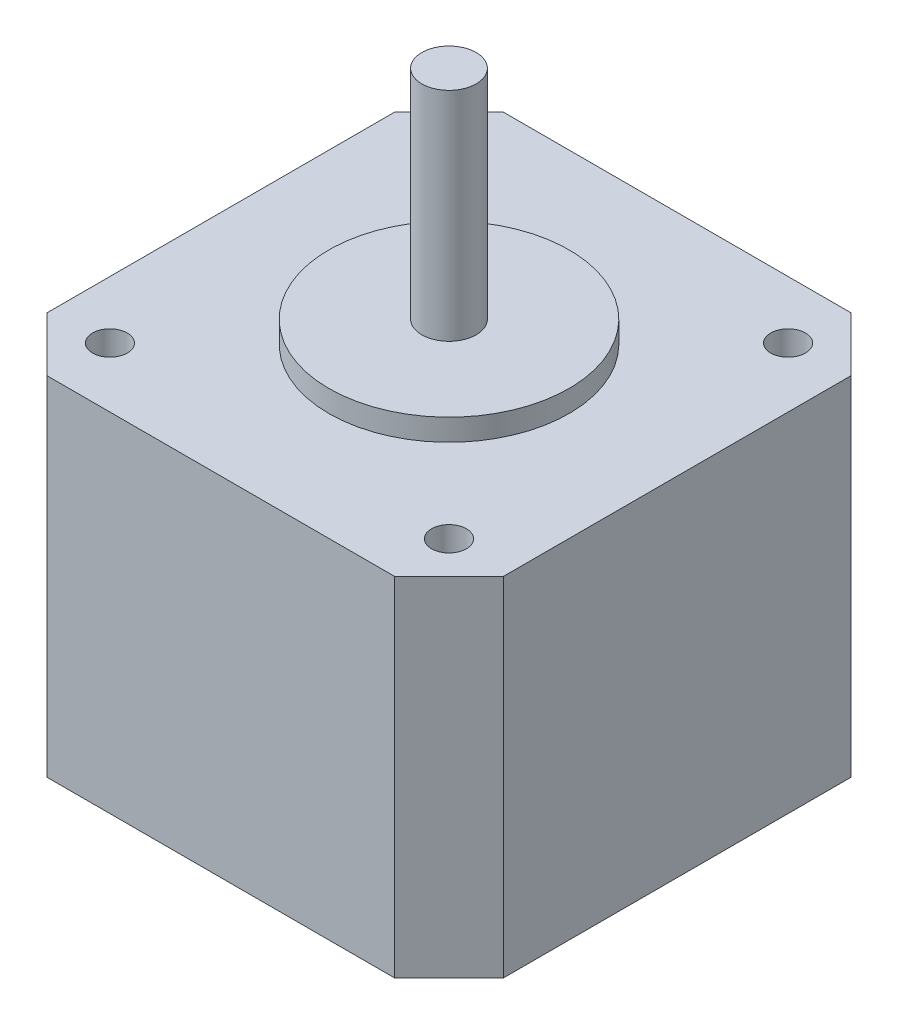
SolidWorks part; units mm, degrees
ref_plane "Front Plane" through (0, 0, 0) normal (0, 0, 1) x (1, 0, 0)
ref_plane "Top Plane" through (0, 0, 0) normal (0, 1, 0) x (1, 0, 0)
ref_plane "Right Plane" through (0, 0, 0) normal (1, 0, 0) x (0, 0, -1)
sketch "Sketch1" plane through (0, 0, 0) normal (0, 1, 0) x (1, 0, 0)
  line L1 (-21, -21) -> (21, -21)
  line L2 (-21, -21) -> (-21, 21)
  line L3 (-21, 21) -> (21, 21)
  line L4 (21, -21) -> (21, 21)
  line L5 (-21, -21) -> (21, 21) construction
  line L6 (-21, 21) -> (21, -21) construction
  point P0 (0, 0)
  dimension "D1" = 42
  dimension "D2" = 42
extrude "Boss-Extrude1" add sketch "Sketch1" along normal blind 32
chamfer "Chamfer1" distance 5 angle 45 4 edges at (-21, 16, -21) (21, 16, -21) (21, 16, 21) (-21, 16, 21)
sketch "Sketch2" plane through (0, 32, 0) normal (0, 1, 0) x (1, 0, 0)
  circle A0 centre (0, 0) radius 11.05
  dimension "D1" = 22.1
extrude "Boss-Extrude2" add sketch "Sketch2" along normal blind 2
sketch "Sketch3" plane through (0, 34, 0) normal (0, 1, 0) x (1, 0, 0)
  circle A0 centre (0, 0) radius 2.5
  dimension "D1" = 5
extrude "Boss-Extrude3" add sketch "Sketch3" along normal blind 20
sketch "Sketch4" plane through (0, 32, 0) normal (0, 1, 0) x (1, 0, 0)
  line L1 (15.7, -15.7) -> (-15.7, -15.7) construction
  line L2 (15.7, -15.7) -> (15.7, 15.7) construction
  line L3 (15.7, 15.7) -> (-15.7, 15.7) construction
  line L4 (-15.7, -15.7) -> (-15.7, 15.7) construction
  line L5 (15.7, -15.7) -> (-15.7, 15.7) construction
  line L6 (15.7, 15.7) -> (-15.7, -15.7) construction
  circle A0 centre (-15.7, 15.7) radius 1.6
  circle A1 centre (15.5, 15.7) radius 1.6
  circle A2 centre (15.5, -15.5) radius 1.6
  circle A3 centre (-15.7, -15.5) radius 1.6
  point P0 (0, 0)
  dimension "D3" = 3.2
  dimension "D1" = 31.4
  dimension "D2" = 31.4
  dimension "D4" = 2
  dimension "D5" = 2
extrude "Cut-Extrude1" cut sketch "Sketch4" against normal blind 5
